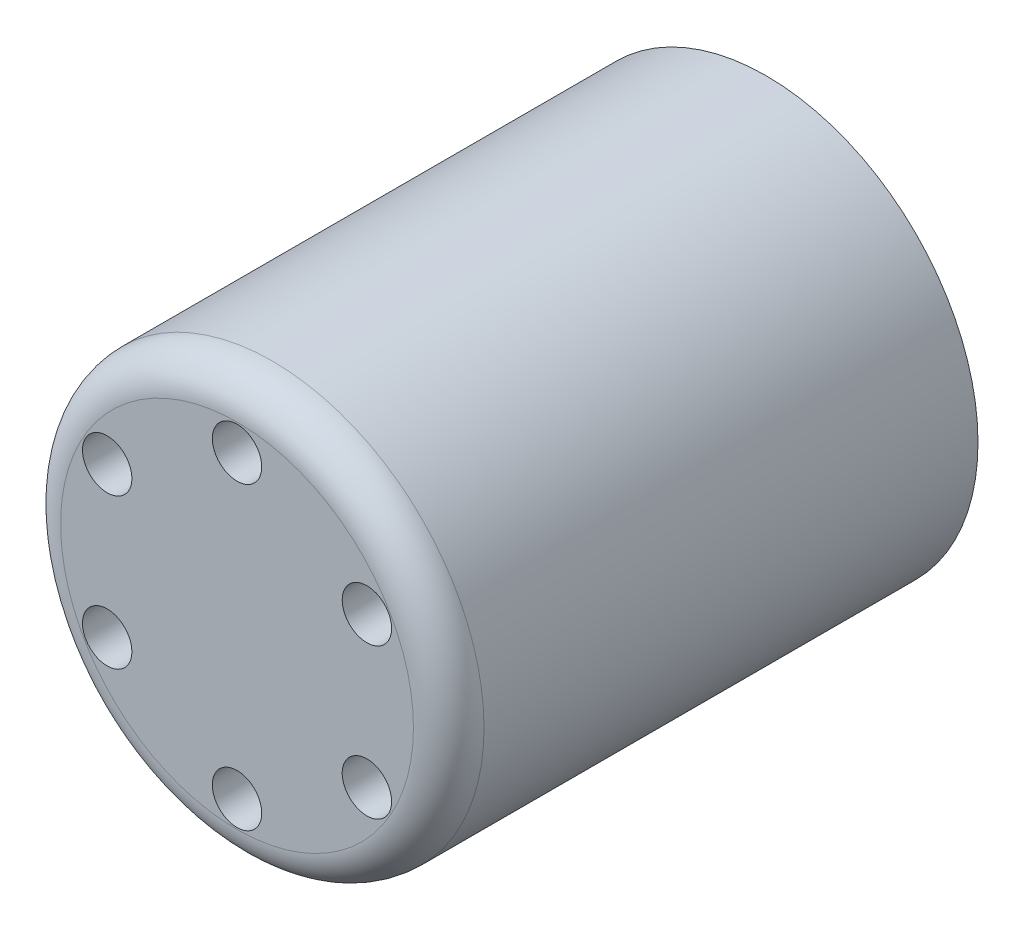
SolidWorks part; units mm, degrees
ref_plane "Front Plane" through (0, 0, 0) normal (0, 0, 1) x (1, 0, 0)
ref_plane "Top Plane" through (0, 0, 0) normal (0, 1, 0) x (1, 0, 0)
ref_plane "Right Plane" through (0, 0, 0) normal (1, 0, 0) x (0, 0, -1)
sketch "Sketch1" plane through (0, 0, 0) normal (0, 0, 1) x (1, 0, 0)
  circle A0 centre (0, 0) radius 6
  dimension "D1" = 12
extrude "Boss-Extrude1" add sketch "Sketch1" along normal blind 15
sketch "Sketch2" plane through (0, 0, 15) normal (0, 0, 1) x (1, 0, 0)
  circle A0 centre (0, 0) radius 4.25
  circle A1 centre (0, 4.25) radius 0.7
  dimension "D1" = 8.5
  dimension "D2" = 1.4
extrude "Cut-Extrude1" cut sketch "Sketch2" against normal blind 3 contours A0 A1 | A0 A1
pattern_circular "CirPattern1" count 6 over 360 about axis through (0, 0, 0) along (0, 0, 1) of "Cut-Extrude1"
fillet "Fillet1" radius 1 1 edges at (6, 0, 15)
